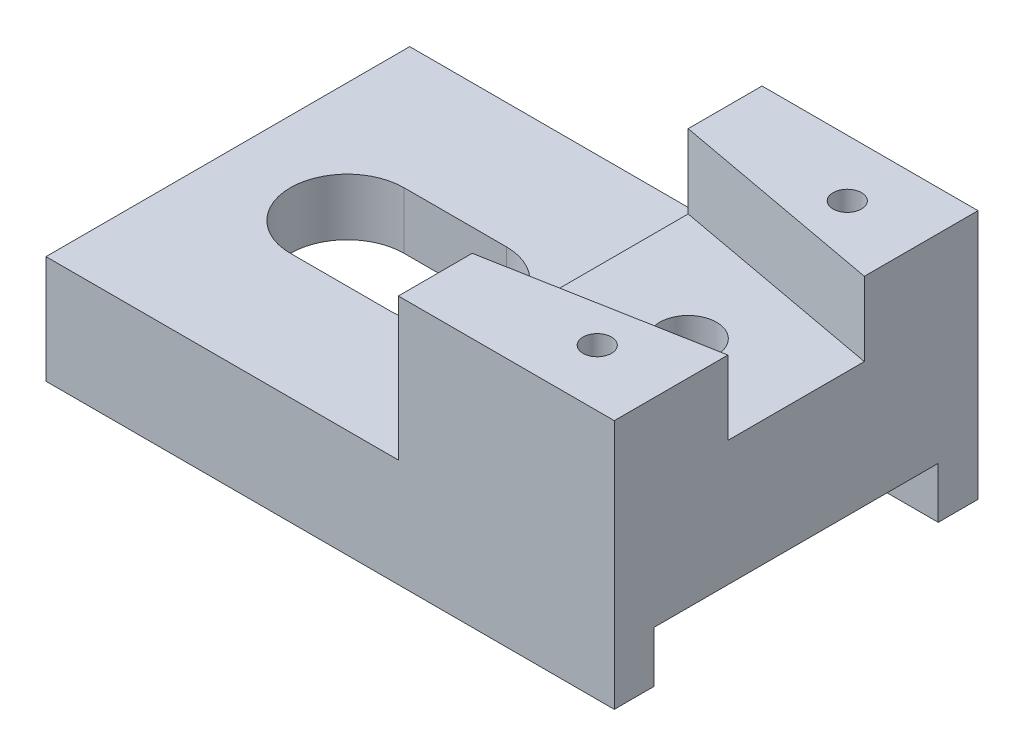
SolidWorks part; units mm, degrees
ref_plane "Front Plane" through (0, 0, 0) normal (0, 0, 1) x (1, 0, 0)
ref_plane "Top Plane" through (0, 0, 0) normal (0, 1, 0) x (1, 0, 0)
ref_plane "Right Plane" through (0, 0, 0) normal (1, 0, 0) x (0, 0, -1)
sketch "Sketch1" plane through (0, 0, 0) normal (0, 0, 1) x (1, 0, 0)
  line L1 (-44.6089, -24.1015) -> (55.3911, -24.1015)
  line L2 (-44.6089, -24.1015) -> (-44.6089, -5.1015)
  line L3 (-44.6089, -5.1015) -> (55.3911, -5.1015)
  line L4 (55.3911, -24.1015) -> (55.3911, -5.1015)
  line L5 (55.3911, -5.1015) -> (17.3911, -5.1015)
  line L6 (55.3911, -5.1015) -> (55.3911, 19.8985)
  line L7 (55.3911, 19.8985) -> (17.3911, 19.8985)
  line L8 (17.3911, -5.1015) -> (17.3911, 19.8985)
  dimension "D1" = 100
  dimension "D2" = 19
  dimension "D3" = 25
  dimension "D4" = 38
extrude "Boss-Extrude1" add sketch "Sketch1" against normal blind 64 contours L1 L4 L3 L2 | L8 L3 L6 L7
sketch "Sketch2" plane through (0, 19.8985, 0) normal (0, 1, 0) x (1, 0, 0)
  line L0 (55.3911, 44) -> (55.3911, 20)
  line L3 (17.3911, 51) -> (17.3911, 13)
  line L5 (17.3911, 13) -> (55.3911, 20)
  line L7 (17.3911, 51) -> (55.3911, 44)
extrude "Cut-Extrude1" cut sketch "Sketch2" against normal blind 13
sketch "Sketch3" plane through (0, -5.1015, 0) normal (0, 1, 0) x (1, 0, 0)
  line L0 (-23.6089, 42) -> (-5.6089, 42)
  line L8 (-23.6089, 22) -> (-5.6089, 22)
  arc A4 (-23.6089, 42) -> (-23.6089, 22) centre (-23.6089, 32) ccw
  arc A5 (-5.6089, 42) -> (-5.6089, 22) centre (-5.6089, 32) cw
extrude "Cut-Extrude2" cut sketch "Sketch3" against normal through all
sketch "Sketch5" plane through (-44.6089, 0, 0) normal (-1, 0, 0) x (0, 0, 1)
  line L1 (-14.0438, -15.1015) -> (-7, -15.1015)
  line L2 (-52.2876, -15.1015) -> (-57, -15.1015)
  line L3 (-57, -24.1015) -> (-7, -24.1015)
  line L5 (-7, -24.1015) -> (-7, -15.1015)
  line L6 (-57, -24.1015) -> (-57, -15.1015)
  line L7 (-52.2876, -15.1015) -> (-14.0438, -15.1015)
extrude "Cut-Extrude3" cut sketch "Sketch5" against normal through all
sketch "Sketch6" plane through (0, 19.8985, 0) normal (0, 1, 0) x (1, 0, 0)
  line L2 (42.3911, 64) -> (42.3911, 54) construction
  line L3 (55.3911, 54) -> (42.3911, 54) construction
  line L5 (42.3911, 0) -> (42.3911, 10) construction
  line L6 (55.3911, 10) -> (42.3911, 10) construction
hole_wizard "Tap Drill for M6 Tap1" positions "Sketch7" profile "Sketch8" hole size "M6" standard "ISO"
sketch "Sketch7" plane through (0, 19.8985, 0) normal (0, 1, 0) x (1, 0, 0)
  point P0 (42.3911, 54)
  point P3 (42.3911, 10)
sketch "Sketch8" plane through (42.3911, 19.8985, -54) normal (1, 0, 0) x (0, 0, 1)
  line L0 (0, 0) -> (0, 21.5022)
  line L1 (0, 21.5022) -> (2.5, 20)
  line L2 (2.5, 20) -> (2.5, 0)
  line L5 (2.5, 0) -> (0, 0)
  line L10 (0, 21.5022) -> (-2.5, 20) construction
  line L11 (0, -6.35) -> (0, 107.95) construction
  dimension "Hole Dia." = 5
  dimension "Hole Depth" = 20
  dimension "Drill Angle" = 118
cosmetic thread "Cosmetic Thread1" parameters "D2"=6
cosmetic thread "Cosmetic Thread2" parameters "D2"=6
sketch "Sketch9" plane through (0, 6.8985, 0) normal (0, 1, 0) x (1, 0, 0)
  circle A1 centre (36.3911, 32) radius 5
  dimension "D1" = 10
extrude "Cut-Extrude4" cut sketch "Sketch9" against normal through all
